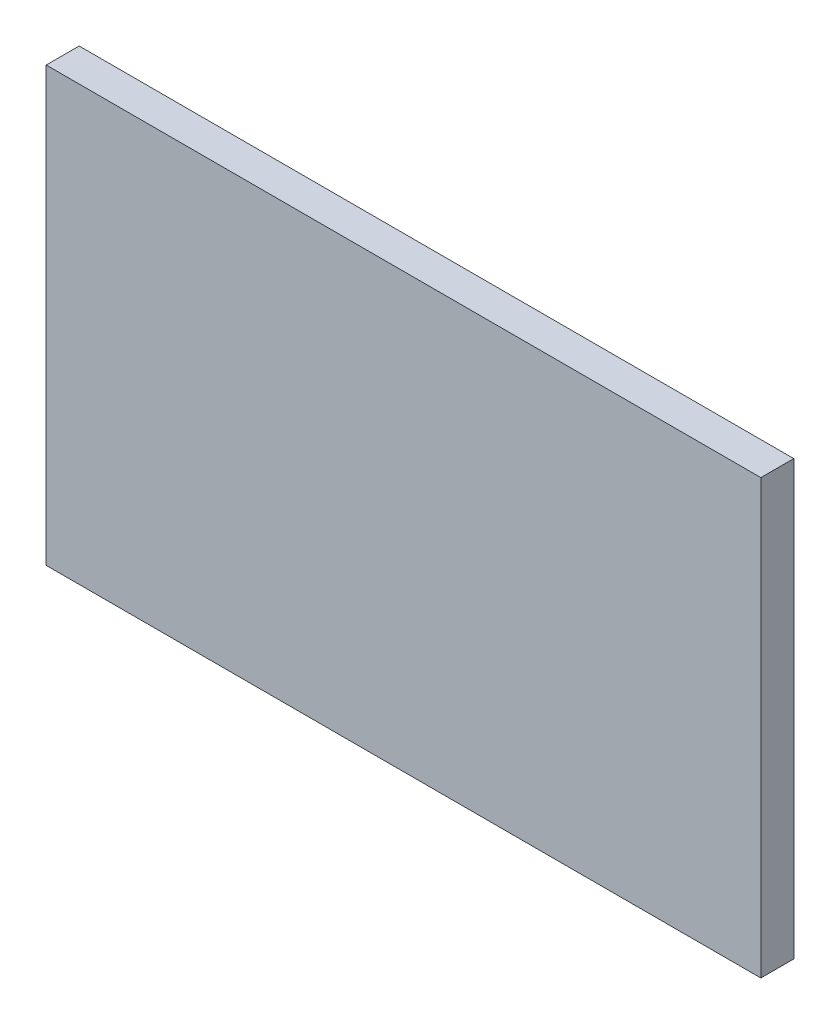
SolidWorks part; units mm, degrees
ref_plane "Plan de face" through (0, 0, 0) normal (0, 0, 1) x (1, 0, 0)
ref_plane "Plan de dessus" through (0, 0, 0) normal (0, 1, 0) x (1, 0, 0)
ref_plane "Plan de droite" through (0, 0, 0) normal (1, 0, 0) x (0, 0, -1)
sketch "Esquisse1" plane through (0, 0, 0) normal (0, 0, 1) x (1, 0, 0)
  line L1 (0, 0) -> (164.9, 0)
  line L2 (0, 0) -> (0, 100)
  line L3 (0, 100) -> (164.9, 100)
  line L4 (164.9, 0) -> (164.9, 100)
  dimension "D1" = 164.9
  dimension "D2" = 100
extrude "Boss.-Extru.1" add sketch "Esquisse1" along normal blind 7.6
